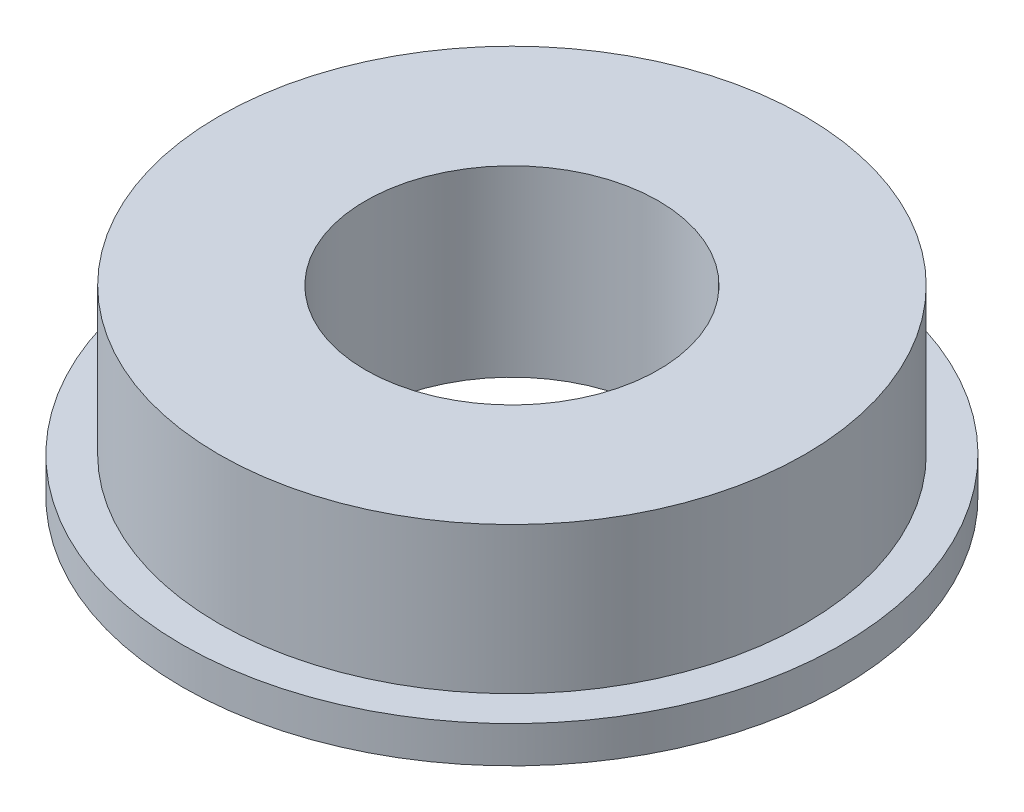
SolidWorks part; units mm, degrees
ref_plane "前视基准面" through (0, 0, 0) normal (0, 0, 1) x (1, 0, 0)
ref_plane "上视基准面" through (0, 0, 0) normal (0, 1, 0) x (1, 0, 0)
ref_plane "右视基准面" through (0, 0, 0) normal (1, 0, 0) x (0, 0, -1)
sketch "草图1" plane through (0, 0, 0) normal (0, 1, 0) x (1, 0, 0)
  circle A0 centre (0, 0) radius 4
  circle A1 centre (0, 0) radius 9
  dimension "D1" = 8
  dimension "D2" = 18
extrude "凸台-拉伸1" add sketch "草图1" along normal blind 5
sketch "草图2" plane through (0, 5, 0) normal (0, 1, 0) x (1, 0, 0)
  circle A0 centre (0, 0) radius 9
  circle A1 centre (0, 0) radius 8
  dimension "D1" = 1
  dimension "D2" = 18
extrude "切除-拉伸1" cut sketch "草图2" against normal blind 4
